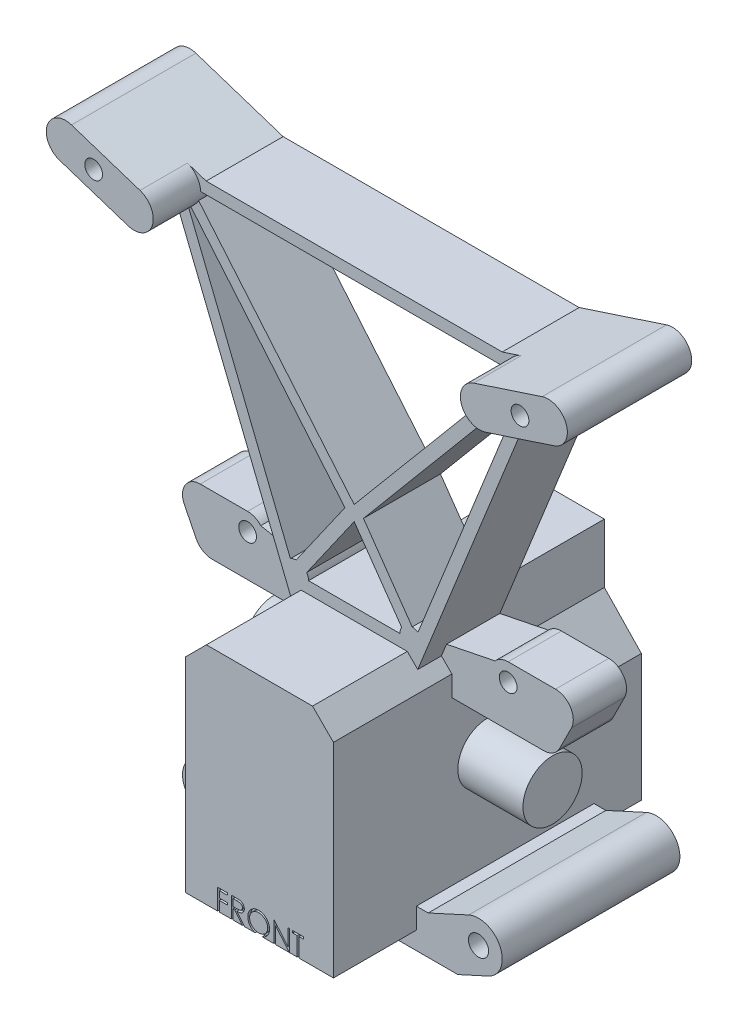
SolidWorks part; units mm, degrees
ref_plane "Front Plane" through (0, 0, 0) normal (0, 0, 1) x (1, 0, 0)
ref_plane "Top Plane" through (0, 0, 0) normal (0, 1, 0) x (1, 0, 0)
ref_plane "Right Plane" through (0, 0, 0) normal (1, 0, 0) x (0, 0, -1)
sketch "Sketch1" plane through (0, 0, 0) normal (1, 0, 0) x (0, 0, -1)
  circle A0 centre (0, 0) radius 5
  dimension "D1" = 10
extrude "Driveline Axis" add sketch "Sketch1" along normal mid plane 47 contours A0
sketch "Sketch2" plane through (0, 0, 0) normal (0, 0, 1) x (1, 0, 0)
  line L0 (-12.5, -20) -> (-12.5, 14.4645)
  line L1 (-12.5, 14.4645) -> (-8.9645, 18)
  line L2 (-8.9645, 18) -> (8.9645, 18)
  line L3 (8.9645, 18) -> (12.5, 14.4645)
  line L4 (12.5, 14.4645) -> (12.5, -20)
  line L5 (12.5, -20) -> (-12.5, -20)
  dimension "D1" = 20
  dimension "D2" = 18
  dimension "D3" = 5
  dimension "D4" = 5
  dimension "D5" = 25
  dimension "D6" = 12.5
extrude "Dummy Boss" add sketch "Sketch2" along normal mid plane 52
ref_plane "Pin Base Plane" through (0, 0, -18) normal (0, 0, -1) x (-1, 0, 0)
sketch "Sketch3" plane through (0, 0, -18) normal (0, 0, -1) x (-1, 0, 0)
  line L0 (-19.5, -23) -> (19.5, -23)
  line L1 (19.5, -23) -> (24.6641, -20.6374)
  line L2 (21.3359, -13.3626) -> (14.5, -16.49)
  line L3 (14.5, -16.49) -> (12.5, -16.49)
  line L4 (12.5, 14.4645) -> (12.5, -20) construction
  line L5 (12.5, -16.49) -> (12.5, -20)
  line L6 (12.5, -20) -> (-12.5, -20)
  line L7 (12.5, -20) -> (-12.5, -20) construction
  line L8 (0, -20) -> (0, -23) construction
  line L9 (-12.5, -16.49) -> (-12.5, -20)
  line L10 (-14.5, -16.49) -> (-12.5, -16.49)
  line L11 (-21.3359, -13.3626) -> (-14.5, -16.49)
  line L12 (-19.5, -23) -> (-24.6641, -20.6374)
  arc A0 (24.6641, -20.6374) -> (21.3359, -13.3626) centre (23, -17) ccw
  arc A1 (-24.6641, -20.6374) -> (-21.3359, -13.3626) centre (-23, -17) cw
  dimension "D3" = 4
  dimension "D1" = 17
  dimension "D2" = 23
  dimension "D4" = 3
  dimension "D5" = 2
  dimension "D6" = 7
extrude "Pin Base" add sketch "Sketch3" against normal blind 30
hole_wizard "Pin Holes" positions "Sketch5" profile "Sketch7" hole size "M3" standard "ANSI Metric" end condition through all
sketch "Sketch5" plane through (0, 0, -18) normal (0, 0, -1) x (-1, 0, 0)
  arc A0 (24.6641, -20.6374) -> (21.3359, -13.3626) centre (23, -17) ccw construction
  arc A1 (-21.3359, -13.3626) -> (-24.6641, -20.6374) centre (-23, -17) ccw construction
  point P0 (-23, -17)
  point P2 (23, -17)
sketch "Sketch7" plane through (23, -17, -18) normal (1, 0, 0) x (0, 1, 0)
  line L0 (0, 0) -> (0, 44)
  line L1 (0, 44) -> (1.7, 44)
  line L2 (1.7, 44) -> (1.7, 0)
  line L5 (1.7, 0) -> (0, 0)
  line L11 (0, -6.35) -> (0, 107.95) construction
  dimension "Thru Hole Dia." = 3.4
  dimension "Thru Hole Depth" = 44
sketch "Sketch8" plane through (0, 0, 0) normal (0, 0, 1) x (1, 0, 0)
  line L0 (-10.7322, 16.2322) -> (-30.2017, 64.6764)
  line L1 (-8.9645, 18) -> (-12.5, 14.4645) construction
  line L2 (-30.2017, 64.6764) -> (-41.7642, 68.4713)
  line L3 (-39.7372, 74.6471) -> (-25, 69.8103)
  line L4 (9.7949, 21.9984) -> (1.5643, 33.7528)
  line L5 (-25, 69.8103) -> (25, 69.8103)
  line L6 (0, 69.8103) -> (0, 18) construction
  line L7 (8.9645, 18) -> (-8.9645, 18) construction
  line L8 (8.9645, 18) -> (-8.9645, 18)
  line L9 (-8.9645, 18) -> (-10.7322, 16.2322)
  line L10 (7.7145, 20) -> (-7.7145, 20)
  line L11 (-10.773, 21.6969) -> (-28.5371, 65.8977)
  line L12 (-8.0147, 21.0539) -> (0, 32.5)
  line L13 (-9.7949, 21.9984) -> (-1.5643, 33.7528)
  line L14 (-1.5643, 33.7528) -> (-28.5371, 65.8977)
  line L15 (-27.5311, 67.8103) -> (0, 35)
  line L16 (8.0147, 21.0539) -> (0, 32.5)
  line L17 (-27.5311, 67.8103) -> (27.5311, 67.8103)
  line L18 (8.9645, 18) -> (10.7322, 16.2322)
  line L19 (27.5311, 67.8103) -> (0, 35)
  line L20 (1.5643, 33.7528) -> (28.5371, 65.8977)
  line L21 (10.773, 21.6969) -> (28.5371, 65.8977)
  line L22 (10.7322, 16.2322) -> (30.2017, 64.6764)
  line L23 (30.2017, 64.6764) -> (41.7642, 68.4713)
  line L24 (39.7372, 74.6471) -> (25, 69.8103)
  arc A0 (-41.7642, 68.4713) -> (-39.7372, 74.6471) centre (-40.7507, 71.5592) cw
  arc A1 (-7.7145, 20) -> (-8.0147, 21.0539) centre (-9.7145, 20) ccw
  arc A2 (-9.7949, 21.9984) -> (-10.773, 21.6969) centre (-9.7145, 20) ccw
  circle A4 centre (-36, 70) radius 1.5
  arc A6 (9.7949, 21.9984) -> (10.773, 21.6969) centre (9.7145, 20) cw
  arc A7 (7.7145, 20) -> (8.0147, 21.0539) centre (9.7145, 20) cw
  arc A8 (41.7642, 68.4713) -> (39.7372, 74.6471) centre (40.7507, 71.5592) ccw
  circle A10 centre (36, 70) radius 1.5
  point P32 (-5.6796, 27.8756)
  point P50 (0, 20)
  point P52 (0, 67.8103)
  dimension "D1" = 2
  dimension "D6" = 2
  dimension "D10" = 3.25
  dimension "D13" = 3
  dimension "D2" = 2
  dimension "D3" = 2
  dimension "D4" = 2
  dimension "D5" = 2
  dimension "D7" = 0.75
  dimension "D8" = 2
  dimension "D9" = 36
  dimension "D14" = 5
  dimension "D16" = 3.25
  dimension "D18" = 70
  dimension "D19" = 113.105
  dimension "D20" = 48.4442
  dimension "D21" = 105
  dimension "D22" = 55
  dimension "D23" = 12.5
  dimension "D24" = 2.5
  dimension "D25" = 25
extrude "Uprights" add sketch "Sketch8" along normal blind 10 and the other way blind 3 contours A2 L13 L14 L11 | L17 L6 L19 | L6 L17 L15 | L4 A6 L21 L20 | L16 L6 L10 A7 | L6 L12 A1 L10 | A4 | A10 | L22 L23 A8 L24 L5 L3 A0 L2 L0 L9 L8 L18
sketch "Sketch9" plane through (0, 0, 10) normal (0, 0, 1) x (1, 0, 0)
  line L0 (-30.2017, 64.6764) -> (-41.7642, 68.4713)
  line L1 (-39.7372, 74.6471) -> (-28.1748, 70.8523)
  line L2 (-39.7372, 74.6471) -> (-25, 69.8103) construction
  line L3 (28.1748, 70.8523) -> (39.7372, 74.6471)
  line L4 (39.7372, 74.6471) -> (25, 69.8103) construction
  line L5 (41.7642, 68.4713) -> (30.2017, 64.6764)
  circle A0 centre (-36, 70) radius 1.5
  circle A1 centre (36, 70) radius 1.5
  circle A2 centre (36, 70) radius 1.5 construction
  circle A3 centre (-36, 70) radius 1.5 construction
  arc A4 (-41.7642, 68.4713) -> (-39.7372, 74.6471) centre (-40.7507, 71.5592) cw
  arc A5 (-39.7372, 74.6471) -> (-41.7642, 68.4713) centre (-40.7507, 71.5592) ccw construction
  arc A6 (-28.1748, 70.8523) -> (-30.2017, 64.6764) centre (-29.1882, 67.7644) cw
  arc A7 (39.7372, 74.6471) -> (41.7642, 68.4713) centre (40.7507, 71.5592) cw
  arc A8 (30.2017, 64.6764) -> (28.1748, 70.8523) centre (29.1882, 67.7644) cw
extrude "Shock Mount" add sketch "Sketch9" along normal blind 8 and the other way blind 13
sketch "Sketch10" plane through (0, 0, 0) normal (0, 0, 1) x (1, 0, 0)
  line L0 (28, 11) -> (9.8033, 11)
  line L1 (-9.8033, 18) -> (-19.7822, 20.0202)
  line L2 (30.6833, 12.6584) -> (32.6833, 16.6584)
  line L3 (30, 21) -> (22, 21)
  line L4 (0, 41.2363) -> (0, 7.9844) construction
  line L5 (9.8033, 11) -> (9.8033, 18)
  line L6 (9.8033, 18) -> (19.7822, 20.0202)
  line L7 (-9.8033, 11) -> (-9.8033, 18)
  line L8 (-28, 11) -> (-9.8033, 11)
  line L9 (-30.6833, 12.6584) -> (-32.6833, 16.6584)
  line L10 (-30, 21) -> (-22, 21)
  arc A0 (28, 11) -> (30.6833, 12.6584) centre (28, 14) ccw
  circle A1 centre (22, 18) radius 1.5
  arc A2 (19.7822, 20.0202) -> (22, 21) centre (22, 18) cw
  arc A3 (30, 21) -> (32.6833, 16.6584) centre (30, 18) cw
  circle A4 centre (30, 18) radius 1.5 construction
  circle A5 centre (-30, 18) radius 1.5 construction
  arc A6 (-28, 11) -> (-30.6833, 12.6584) centre (-28, 14) cw
  arc A7 (-30, 21) -> (-32.6833, 16.6584) centre (-30, 18) ccw
  arc A8 (-19.7822, 20.0202) -> (-22, 21) centre (-22, 18) ccw
  circle A9 centre (-22, 18) radius 1.5
  dimension "D1" = 3
  dimension "D2" = 3
  dimension "D3" = 3
  dimension "D4" = 4
  dimension "D6" = 3
  dimension "D8" = 3
  dimension "D5" = 8
  dimension "D7" = 2
  dimension "D9" = 44
  dimension "D10" = 18
extrude "Turnbuckle Mounts" add sketch "Sketch10" against normal blind 3 and the other way blind 6
sketch "Sketch11" plane through (0, 0, -26) normal (0, 0, -1) x (-1, 0, 0)
  line L0 (-12.5, 1.4645) -> (-6.25, 8)
  line L1 (-12.5, -20) -> (-12.5, 14.4645) construction
  line L2 (-6.25, 8) -> (-6.25, 18)
  line L3 (-8.9645, 18) -> (8.9645, 18) construction
  line L4 (5.75, 18) -> (8.9645, 18)
  line L5 (-8.9645, 18) -> (8.9645, 18) construction
  line L6 (5.75, 18) -> (5.75, 8)
  line L7 (5.75, 8) -> (12.5, 1.5449)
  line L8 (12.5, 14.4645) -> (12.5, -20) construction
  line L9 (-12.5, 1.4645) -> (-12.5, 14.4645)
  line L10 (-6.25, 18) -> (-8.9645, 18)
  line L11 (8.9645, 18) -> (12.5, 14.4645)
  line L12 (12.5, 14.4645) -> (12.5, 11) construction
  line L13 (8.9645, 18) -> (12.5, 14.4645) construction
  line L14 (12.5, 14.4645) -> (12.5, 1.5449)
  line L15 (12.5, 1.5449) -> (12.5075, 1.5371)
  line M5 (12.5, -20) -> (12.5, 14.4645)
  line M6 (12.5, 14.4645) -> (8.9645, 18)
  line M7 (8.9645, 18) -> (-8.9645, 18)
  line M8 (-8.9645, 18) -> (-12.5, 14.4645)
  line M9 (-12.5, 14.4645) -> (-12.5, -20)
  dimension "D1" = 12
  dimension "D2" = 10
  dimension "D3" = 6.25
  dimension "D4" = 13
extrude "Turnbuckle Room" cut sketch "Sketch11" against normal blind 23 and the other way through all contours L6 L7 M5 M6 M7 | L0 L2 M7 M8 M9
sketch "Sketch12" plane through (0, 0, 26) normal (0, 0, 1) x (1, 0, 0)
  text T0 "FRONT"
extrude "Cut-Extrude1" cut sketch "Sketch12" against normal blind 0.5
